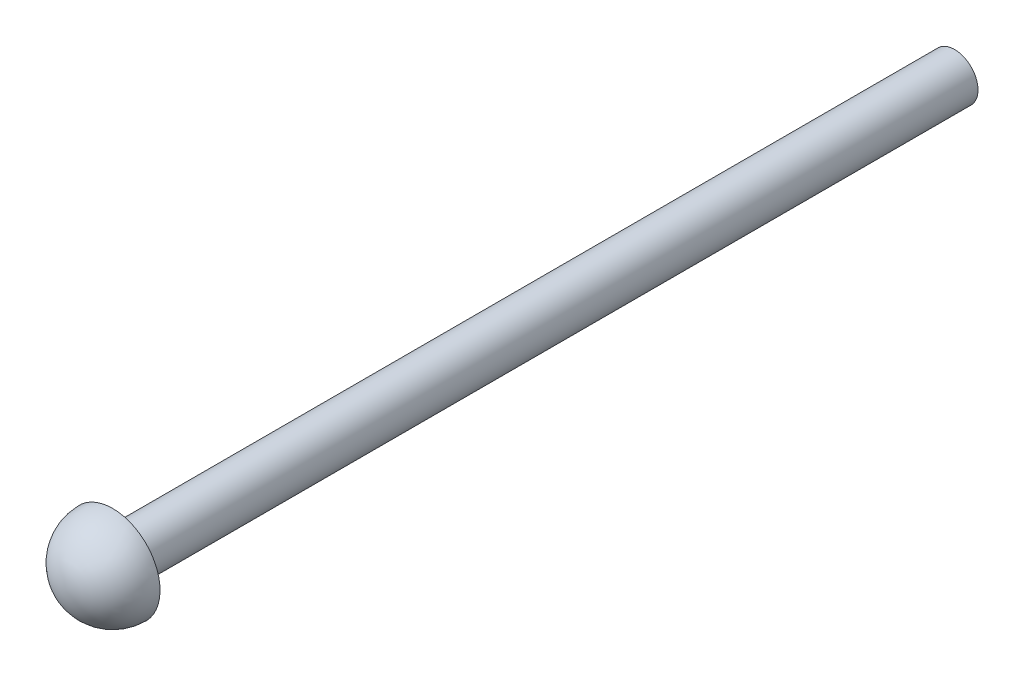
SolidWorks part; units mm, degrees
ref_plane "Front Plane" through (0, 0, 0) normal (0, 0, 1) x (1, 0, 0)
ref_plane "Top Plane" through (0, 0, 0) normal (0, 1, 0) x (1, 0, 0)
ref_plane "Right Plane" through (0, 0, 0) normal (1, 0, 0) x (0, 0, -1)
sketch "Sketch1" plane through (0, 0, 0) normal (0, 0, 1) x (1, 0, 0)
  circle A0 centre (0, 0) radius 3.175
  dimension "D1" = 6.35
extrude "Boss-Extrude1" add sketch "Sketch1" along normal blind 114.3
sketch "Sketch3" plane through (0, 0, 0) normal (1, 0, 0) x (0, 0, -1)
  line L1 (-114.3, 6.35) -> (-114.3, -6.477)
  line L2 (-114.3, -0.0635) -> (-120.7135, -0.0635)
  line L3 (-114.3, 3.175) -> (-114.3, -3.175) construction
  arc A0 (-114.3, 6.35) -> (-114.3, -6.477) centre (-114.3, -0.0635) ccw
  point P7 (-114.3, 3.175)
  point P13 (-114.3, -3.175)
  dimension "D1" = 3.175
  dimension "D2" = 3.302
revolve "Revolve1" add sketch "Sketch3" angle 360 about L2
equation "\"Thick\"= \"in\""
equation "\"D2@Sketch3\"=\"D1@Sketch3\""
